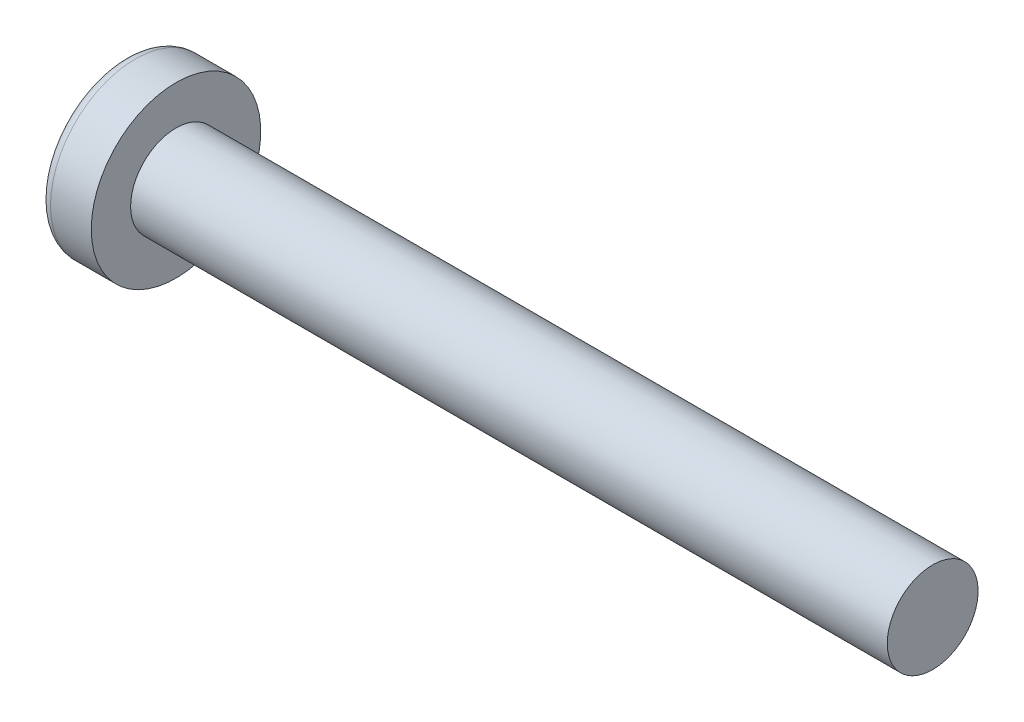
SolidWorks part; units mm, degrees
ref_plane "Plane1" through (0, 0, 0) normal (0, 0, 1) x (1, 0, 0)
ref_plane "Plane2" through (0, 0, 0) normal (0, 1, 0) x (1, 0, 0)
ref_plane "Plane3" through (0, 0, 0) normal (1, 0, 0) x (0, 0, -1)
sketch "BodySke" plane through (0, 0, 0) normal (0, 0, 1) x (1, 0, 0)
  line L0 (2.4, 1.5) -> (2.4, 2.8)
  line L1 (2.9, 6.35) -> (2.9, -3.175) construction
  line L2 (-25.4, 0) -> (127, 0) construction
  line L3 (27.4, 0) -> (0, 0)
  line L4 (2.4, 1.5) -> (27.4, 1.5)
  line L5 (27.4, 1.5) -> (27.4, 0)
  line L6 (1.0534, 2.8) -> (2.4, 2.8)
  line L7 (2.4, -1.5) -> (27.4, -1.5) construction
  line L8 (2.4, 6.35) -> (2.4, -3.175) construction
  arc A0 (0.7472, 2.6293) -> (0, 0) centre (5, 0) ccw
  arc A2 (0.7472, 2.6293) -> (1.0534, 2.8) centre (1.0534, 2.44) cw
  dimension "Head_fillet_rad" = 0.36
  dimension "Head_crown_rad" = 5
  dimension "Head_ht" = 2.4
  dimension "Diameter" = 3
  dimension "Length" = 25
  dimension "Head_dia" = 5.6
  dimension "Advance" = 0.5
  dimension "Thread_nom" = 25
revolve "Base-Revolve" add sketch "BodySke" angle 360 about L2
cosmetic thread "ThreadCosmetic" [suppressed] parameters "Thread_length"=24.5, "Thread_minor"=2.439
sketch "Sketch3" plane through (0, 0, 0) normal (1, 0, 0) x (0, 0, -1)
  line L0 (0.37, -1.45) -> (-0.37, -1.45)
  line L1 (0.37, -1.45) -> (0.37, 1.45)
  line L2 (-0.37, 1.45) -> (0.37, 1.45)
  line L3 (-0.37, 1.45) -> (-0.37, -1.45)
  dimension "D1" = 1.45
  dimension "Cross_dia" = 2.9
  dimension "D2" = 0.37
  dimension "Cross_width" = 0.74
ref_plane "Plane4" through (1.76, 0, 0) normal (1, 0, 0) x (0, 0, -1)
sketch "Sketch4" plane through (1.76, 0, 0) normal (1, 0, 0) x (0, 0, -1)
  line L0 (0.185, -0.185) -> (-0.185, -0.185)
  line L1 (0.185, -0.185) -> (0.185, 0.185)
  line L2 (-0.185, 0.185) -> (0.185, 0.185)
  line L3 (-0.185, 0.185) -> (-0.185, -0.185)
  dimension "D1" = 0.37
  dimension "D2" = 0.37
  dimension "D3" = 0.185
  dimension "D4" = 0.185
loft "Cut-Loft1" cut profiles "Sketch3", "Sketch4"
pattern_circular "CirPattern1" count 2 every 90 about axis through (-25.4, 0, 0) along (1, 0, 0)
sketch "ThdSchSke" plane through (0, 0, 0) normal (0, 0, 1) x (1, 0, 0)
  line L0 (2.9, -1.2195) -> (2.7036, -1.5)
  line L1 (2.9, -1.2195) -> (3.0964, -1.5)
  line L2 (3.0964, -1.5) -> (3.0964, -1.875)
  line L3 (-3.175, 0) -> (5.1513, 0) construction
  line L5 (3.0964, -1.875) -> (2.7036, -1.875)
  line L6 (2.7036, -1.875) -> (2.7036, -1.5)
  dimension "Thread_minor" = 2.439
  dimension "Diameter" = 3
  dimension "Start" = 2.9
  dimension "SideAngle" = 55
  dimension "VeeAngle" = 70
  dimension "Overcut" = 3.75
revolve "ThreadSchematic" [suppressed] cut sketch "ThdSchSke" angle 360 about L3
pattern_linear "ThdSchPat" [suppressed]
equation "\"D1@Sketch3\" = \"Cross_dia@Sketch3\" / 2"
equation "\"D2@Sketch3\" = \"Cross_width@Sketch3\" / 2"
equation "\"D1@Sketch4\" = \"Cross_width@Sketch3\" *.5"
equation "\"D2@Sketch4\" = \"D1@Sketch4\""
equation "\"D3@Sketch4\" = \"D1@Sketch4\" / 2"
equation "\"D4@Sketch4\" = \"D2@Sketch4\" / 2"
equation "\"Thread_length@ThreadCosmetic\" = ((sgn( (\"Length@BodySke\" - \"Advance@BodySke\" ) - \"Thread_nom@BodySke\" )-1)*( (\"Length@BodySke\" - \"Advance@BodySke\" ) - \"Thread_nom@BodySke\" ))/-2+ \"Thread_nom@BodySke\""
equation "\"Thread_minor@ThdSchSke\" = \"Thread_minor@ThreadCosmetic\""
equation "\"Diameter@ThdSchSke\" = \"Diameter@BodySke\""
equation "\"Overcut@ThdSchSke\" = \"Diameter@BodySke\" * 1.25"
equation "\"Start@ThdSchSke\" = \"Head_ht@BodySke\" + \"Length@BodySke\" - \"Thread_length@ThreadCosmetic\"  '---Non-countersunk---"
equation "\"Num_threads@ThdSchPat\" = int( \"Thread_length@ThreadCosmetic\" / \"Advance@BodySke\" + 0.999 )  + 1"
equation "\"Advance@ThdSchPat\" = \"Thread_length@ThreadCosmetic\" /  (\"Num_threads@ThdSchPat\" - 1) 'relax it"
